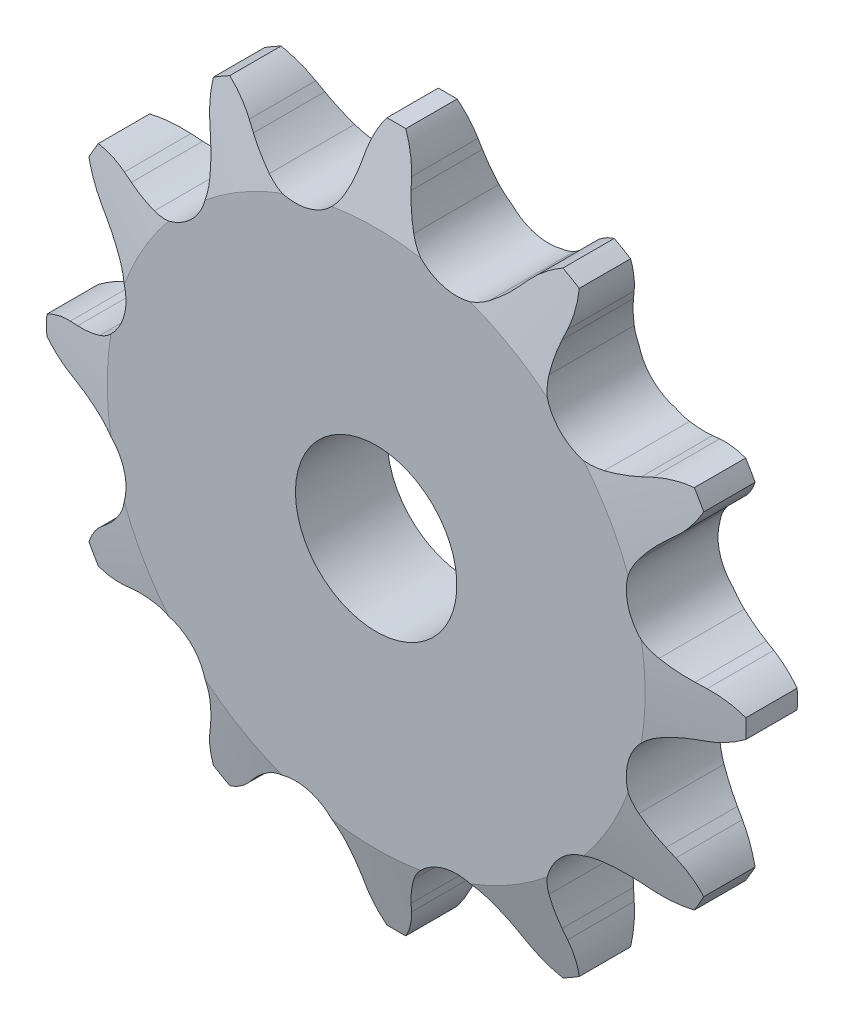
SolidWorks part; units mm, degrees
ref_plane "Front Plane" through (0, 0, 0) normal (0, 0, 1) x (1, 0, 0)
ref_plane "Top Plane" through (0, 0, 0) normal (0, 1, 0) x (1, 0, 0)
ref_plane "Right Plane" through (0, 0, 0) normal (1, 0, 0) x (0, 0, -1)
sketch "Sketch0" plane through (0, 0, 0) normal (0, 0, 1) x (1, 0, 0)
  line L0 (6.35, -23.6985) -> (0, 0) construction
  line L1 (0, 0) -> (17.3485, -17.3485) construction
  line L2 (0, 0) -> (-6.35, -23.6985) construction
  line L3 (6.35, -23.6985) -> (17.3485, -17.3485) construction
  line L4 (6.35, -23.6985) -> (-6.35, -23.6985) construction
  line L5 (10.9724, -22.5882) -> (10.4529, -22.0044)
  line L6 (6.35, -23.6985) -> (0, -25.4) construction
  line L7 (1.7917, -25.0482) -> (1.9497, -24.2829)
  line L8 (0, -23.6985) -> (0, -27.5085) construction
  line L9 (8.656, -20.4053) -> (2.7136, -28.8918) construction
  line L10 (0, 0) -> (0, -23.6985) construction
  line L11 (10.4529, -22.0044) -> (2.7136, -28.8918) construction
  line L12 (0, -27.5085) -> (0, -28.3926) construction
  line L13 (15.9583, -18.1512) -> (10.9724, -22.5882) construction
  circle A0 centre (0, 0) radius 27.5085 construction
  circle A1 centre (0, 0) radius 24.5345 construction
  arc A2 (-6.055, -30.243) -> (20.3653, -23.1637) centre (0, 0) ccw
  circle A3 centre (0, 0) radius 28.3926 construction
  circle A4 centre (6.35, -23.6985) radius 3.9624 construction
  arc A7 (8.656, -20.4053) -> (2.7064, -21.9995) centre (6.35, -23.6985) ccw
  circle A8 centre (6.35, -23.6985) radius 4.0203 construction
  arc A9 (10.9724, -22.5882) -> (20.3653, -23.1637) centre (15.9583, -18.1512) ccw
  arc A10 (10.4529, -22.0044) -> (8.656, -20.4053) centre (2.7136, -28.8918) ccw
  arc A11 (1.7917, -25.0482) -> (-6.055, -30.243) centre (-4.7447, -23.6985) cw
  arc A12 (1.9497, -24.2829) -> (2.7064, -21.9995) centre (12.0958, -26.3779) cw
  dimension "D1" = 4.0203
  dimension "R" = 4.0203
sketch "Sketch1" plane through (0, 0, 0) normal (1, 0, 0) x (0, 0, -1)
  line L0 (3.6068, 0) -> (-3.6068, 0)
  line L1 (-3.6068, 0) -> (-3.6068, 21.1585)
  line L2 (-3.6068, 21.1585) -> (-2.0193, 27.5085)
  line L3 (-2.0193, 27.5085) -> (2.0193, 27.5085)
  line L4 (2.0193, 27.5085) -> (3.6068, 21.1585)
  line L5 (3.6068, 21.1585) -> (3.6068, 0)
  line L7 (0, 27.5085) -> (0, 0) construction
  line L8 (-3.6068, 21.1585) -> (3.6068, 21.1585) construction
  line L9 (0, 27.5085) -> (0, -27.5085) construction
  line L10 (-3.6068, 21.1585) -> (-3.6068, 27.5085) construction
  line L11 (-3.6068, 27.5085) -> (-2.0193, 27.5085) construction
  line L12 (2.0193, 27.5085) -> (3.6068, 27.5085) construction
  line L13 (3.6068, 27.5085) -> (3.6068, 21.1585) construction
revolve "Revolve1" add sketch "Sketch1" angle 360 mid plane about L0
extrude "Cut-Extrude1" cut sketch "Sketch0" against normal through all and the other way through all
pattern_circular "CirPattern1" count 12 over 360 about axis through (0, 0, 0) along (0, 0, 1) of "Cut-Extrude1"
sketch "Sketch2" plane through (0, 0, 0) normal (0, 0, 1) x (1, 0, 0)
  circle A0 centre (0, 0) radius 6.35 construction
  circle A1 centre (0, 0) radius 30.1625
  circle A2 centre (0, 0) radius 27.559 construction
  dimension "Bore" = 12.7
  dimension "Hub Dia." = 60.325
  dimension "OD" = 55.118
sketch "Sketch3" plane through (0, 0, 0) normal (0, 0, 1) x (1, 0, 0)
  circle A0 centre (0, 0) radius 6.35 construction
  circle A1 centre (0, 0) radius 6.35
  circle A2 centre (0, 0) radius 27.559 construction
  circle A3 centre (0, 0) radius 27.559
extrude "Cut-Extrude2" cut sketch "Sketch3" along normal through all and the other way through all flip side to cut
equation "\"360/N@Sketch0\" = 360/\"Teeth@CirPattern1\""
equation "\"Ds@Sketch0\" = 1.005 * \"Dr@Sketch0\" + 0.003"
equation "\"R@Sketch0\" = 1/2 * \"Ds@Sketch0\""
equation "\"A@Sketch0\" = 35 +  ( 60 / \"Teeth@CirPattern1\" ) "
equation "\"B@Sketch0\" = 18 -  ( 56 / \"Teeth@CirPattern1\" )"
equation "\"ac@Sketch0\" = 0.8 * \"Dr@Sketch0\""
equation "\"ab@Sketch0\" = 1.4 * \"Dr@Sketch0\""
equation "\"J@Sketch0\" = 0.3 * \"Pitch@Sketch0\""
equation "\"h@Sketch1\" = \"Pitch@Sketch0\" / 2"
equation "\"g@Sketch1\" = \"h@Sketch1\" / 4"
